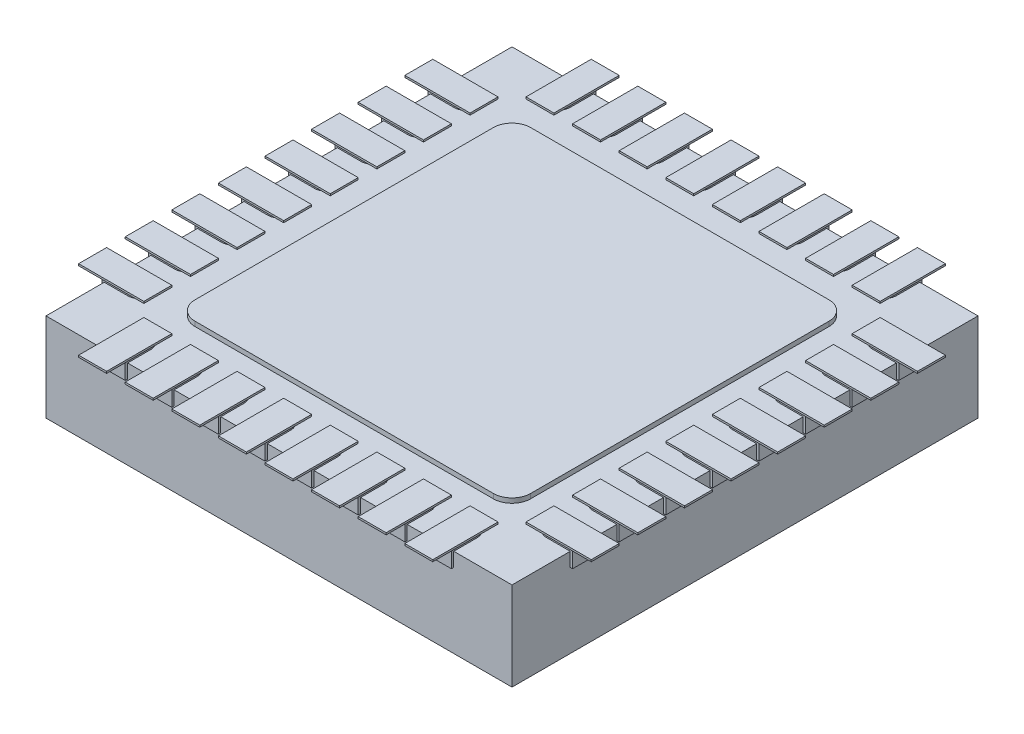
SolidWorks part; units mm, degrees
ref_plane "Front Plane" through (0, 0, 0) normal (0, 0, 1) x (1, 0, 0)
ref_plane "Top Plane" through (0, 0, 0) normal (0, 1, 0) x (1, 0, 0)
ref_plane "Right Plane" through (0, 0, 0) normal (1, 0, 0) x (0, 0, -1)
sketch "Sketch1" plane through (0, 0, 0) normal (0, 1, 0) x (1, 0, 0)
  line L0 (0, -2.75) -> (0, 2.75) construction
  line L1 (-2.525, 2.525) -> (2.525, 2.525)
  line L2 (-2.525, 2.525) -> (-2.525, -2.525)
  line L3 (-2.525, -2.525) -> (2.525, -2.525)
  line L4 (2.525, 2.525) -> (2.525, -2.525)
  line L5 (-2.75, 0) -> (2.75, 0) construction
sketch "Sketch2" plane through (0, 0, 0) normal (0, 1, 0) x (1, 0, 0)
  line L0 (0, -2.75) -> (0, 2.75) construction
  line L1 (-1.6, -1.8) -> (1.6, -1.8)
  line L2 (-1.8, -1.6) -> (-1.8, 1.6)
  line L3 (-1.6, 1.8) -> (1.6, 1.8)
  line L4 (1.8, -1.6) -> (1.8, 1.6)
  line L5 (-2.75, 0) -> (2.75, 0) construction
  line L6 (-1.875, -2.25) -> (-1.875, -2.525)
  line L8 (-1.875, -2.525) -> (-1.625, -2.525)
  line L9 (-1.625, -2.525) -> (-1.625, -2.25)
  line L10 (-1.875, 2.25) -> (-1.875, 2.525)
  line L12 (-1.875, 2.525) -> (-1.625, 2.525)
  line L13 (-1.625, 2.525) -> (-1.625, 2.25)
  line L14 (-1.375, -2.25) -> (-1.375, -2.525)
  line L15 (-1.125, -2.525) -> (-1.125, -2.25)
  line L16 (-1.375, -2.525) -> (-1.125, -2.525)
  line L17 (-1.125, 2.525) -> (-1.125, 2.25)
  line L18 (-1.375, 2.25) -> (-1.375, 2.525)
  line L19 (-1.375, 2.525) -> (-1.125, 2.525)
  line L20 (-0.875, -2.25) -> (-0.875, -2.525)
  line L21 (-0.625, -2.525) -> (-0.625, -2.25)
  line L22 (-0.875, -2.525) -> (-0.625, -2.525)
  line L23 (-0.625, 2.525) -> (-0.625, 2.25)
  line L24 (-0.875, 2.25) -> (-0.875, 2.525)
  line L25 (-0.875, 2.525) -> (-0.625, 2.525)
  line L26 (-0.375, -2.25) -> (-0.375, -2.525)
  line L27 (-0.125, -2.525) -> (-0.125, -2.25)
  line L28 (-0.375, -2.525) -> (-0.125, -2.525)
  line L29 (-0.125, 2.525) -> (-0.125, 2.25)
  line L30 (-0.375, 2.25) -> (-0.375, 2.525)
  line L31 (-0.375, 2.525) -> (-0.125, 2.525)
  line L32 (0.125, -2.25) -> (0.125, -2.525)
  line L33 (0.375, -2.525) -> (0.375, -2.25)
  line L34 (0.125, -2.525) -> (0.375, -2.525)
  line L35 (0.375, 2.525) -> (0.375, 2.25)
  line L36 (0.125, 2.25) -> (0.125, 2.525)
  line L37 (0.125, 2.525) -> (0.375, 2.525)
  line L38 (0.625, -2.25) -> (0.625, -2.525)
  line L39 (0.875, -2.525) -> (0.875, -2.25)
  line L40 (0.625, -2.525) -> (0.875, -2.525)
  line L41 (0.875, 2.525) -> (0.875, 2.25)
  line L42 (0.625, 2.25) -> (0.625, 2.525)
  line L43 (0.625, 2.525) -> (0.875, 2.525)
  line L44 (1.125, -2.25) -> (1.125, -2.525)
  line L45 (1.375, -2.525) -> (1.375, -2.25)
  line L46 (1.125, -2.525) -> (1.375, -2.525)
  line L47 (1.375, 2.525) -> (1.375, 2.25)
  line L48 (1.125, 2.25) -> (1.125, 2.525)
  line L49 (1.125, 2.525) -> (1.375, 2.525)
  line L50 (1.625, -2.25) -> (1.625, -2.525)
  line L51 (1.875, -2.525) -> (1.875, -2.25)
  line L52 (1.625, -2.525) -> (1.875, -2.525)
  line L53 (1.875, 2.525) -> (1.875, 2.25)
  line L54 (1.625, 2.25) -> (1.625, 2.525)
  line L55 (1.625, 2.525) -> (1.875, 2.525)
  line L56 (-2.525, -1.875) -> (-2.245, -1.875)
  line L59 (-2.245, -1.625) -> (-2.525, -1.625)
  line L60 (2.245, -1.875) -> (2.525, -1.875)
  line L62 (2.525, -1.875) -> (2.525, -1.625)
  line L63 (2.525, -1.625) -> (2.245, -1.625)
  line L64 (-2.525, -1.625) -> (-2.525, -1.875)
  line L65 (-2.245, -1.125) -> (-2.525, -1.125)
  line L66 (-2.525, -1.375) -> (-2.245, -1.375)
  line L67 (-2.525, -1.125) -> (-2.525, -1.375)
  line L68 (2.245, -1.375) -> (2.525, -1.375)
  line L69 (2.525, -1.375) -> (2.525, -1.125)
  line L70 (2.525, -1.125) -> (2.245, -1.125)
  line L71 (-2.245, -0.625) -> (-2.525, -0.625)
  line L72 (-2.525, -0.875) -> (-2.245, -0.875)
  line L73 (-2.525, -0.625) -> (-2.525, -0.875)
  line L74 (2.245, -0.875) -> (2.525, -0.875)
  line L75 (2.525, -0.875) -> (2.525, -0.625)
  line L76 (2.525, -0.625) -> (2.245, -0.625)
  line L77 (-2.245, -0.125) -> (-2.525, -0.125)
  line L78 (-2.525, -0.375) -> (-2.245, -0.375)
  line L79 (-2.525, -0.125) -> (-2.525, -0.375)
  line L80 (2.245, -0.375) -> (2.525, -0.375)
  line L81 (2.525, -0.375) -> (2.525, -0.125)
  line L82 (2.525, -0.125) -> (2.245, -0.125)
  line L83 (-2.245, 0.375) -> (-2.525, 0.375)
  line L84 (-2.525, 0.125) -> (-2.245, 0.125)
  line L85 (-2.525, 0.375) -> (-2.525, 0.125)
  line L86 (2.245, 0.125) -> (2.525, 0.125)
  line L87 (2.525, 0.125) -> (2.525, 0.375)
  line L88 (2.525, 0.375) -> (2.245, 0.375)
  line L89 (-2.245, 0.875) -> (-2.525, 0.875)
  line L90 (-2.525, 0.625) -> (-2.245, 0.625)
  line L91 (-2.525, 0.875) -> (-2.525, 0.625)
  line L92 (2.245, 0.625) -> (2.525, 0.625)
  line L93 (2.525, 0.625) -> (2.525, 0.875)
  line L94 (2.525, 0.875) -> (2.245, 0.875)
  line L95 (-2.245, 1.375) -> (-2.525, 1.375)
  line L96 (-2.525, 1.125) -> (-2.245, 1.125)
  line L97 (-2.525, 1.375) -> (-2.525, 1.125)
  line L98 (2.245, 1.125) -> (2.525, 1.125)
  line L99 (2.525, 1.125) -> (2.525, 1.375)
  line L100 (2.525, 1.375) -> (2.245, 1.375)
  line L101 (-2.245, 1.875) -> (-2.525, 1.875)
  line L102 (-2.525, 1.625) -> (-2.245, 1.625)
  line L103 (-2.525, 1.875) -> (-2.525, 1.625)
  line L104 (2.245, 1.625) -> (2.525, 1.625)
  line L105 (2.525, 1.625) -> (2.525, 1.875)
  line L106 (2.525, 1.875) -> (2.245, 1.875)
  line L107 (-2.245, -1.625) -> (-2.245, -1.125) construction
  line L108 (-2.525, 2.525) -> (-2.525, -2.525) construction
  line L109 (-2.525, 2.525) -> (2.525, 2.525) construction
  line L110 (-2.525, -2.525) -> (2.525, -2.525) construction
  line L111 (2.525, 2.525) -> (2.525, -2.525) construction
  arc A0 (1.6, 1.8) -> (1.8, 1.6) centre (1.6, 1.6) cw
  arc A1 (-1.8, 1.6) -> (-1.6, 1.8) centre (-1.6, 1.6) cw
  arc A2 (-1.6, -1.8) -> (-1.8, -1.6) centre (-1.6, -1.6) cw
  arc A3 (1.6, -1.8) -> (1.8, -1.6) centre (1.6, -1.6) ccw
  arc A4 (-1.625, -2.25) -> (-1.875, -2.25) centre (-1.75, -2.25) ccw
  arc A5 (-1.875, 2.25) -> (-1.625, 2.25) centre (-1.75, 2.25) ccw
  arc A6 (-1.125, -2.25) -> (-1.375, -2.25) centre (-1.25, -2.25) ccw
  arc A7 (-1.375, 2.25) -> (-1.125, 2.25) centre (-1.25, 2.25) ccw
  arc A8 (-0.625, -2.25) -> (-0.875, -2.25) centre (-0.75, -2.25) ccw
  arc A9 (-0.875, 2.25) -> (-0.625, 2.25) centre (-0.75, 2.25) ccw
  arc A10 (-0.125, -2.25) -> (-0.375, -2.25) centre (-0.25, -2.25) ccw
  arc A11 (-0.375, 2.25) -> (-0.125, 2.25) centre (-0.25, 2.25) ccw
  arc A12 (0.375, -2.25) -> (0.125, -2.25) centre (0.25, -2.25) ccw
  arc A13 (0.125, 2.25) -> (0.375, 2.25) centre (0.25, 2.25) ccw
  arc A14 (0.875, -2.25) -> (0.625, -2.25) centre (0.75, -2.25) ccw
  arc A15 (0.625, 2.25) -> (0.875, 2.25) centre (0.75, 2.25) ccw
  arc A16 (1.375, -2.25) -> (1.125, -2.25) centre (1.25, -2.25) ccw
  arc A17 (1.125, 2.25) -> (1.375, 2.25) centre (1.25, 2.25) ccw
  arc A18 (1.875, -2.25) -> (1.625, -2.25) centre (1.75, -2.25) ccw
  arc A19 (1.625, 2.25) -> (1.875, 2.25) centre (1.75, 2.25) ccw
  arc A20 (-2.245, -1.875) -> (-2.245, -1.625) centre (-2.245, -1.75) ccw
  arc A21 (2.245, -1.625) -> (2.245, -1.875) centre (2.245, -1.75) ccw
  arc A22 (-2.245, -1.375) -> (-2.245, -1.125) centre (-2.245, -1.25) ccw
  arc A23 (2.245, -1.125) -> (2.245, -1.375) centre (2.245, -1.25) ccw
  arc A24 (-2.245, -0.875) -> (-2.245, -0.625) centre (-2.245, -0.75) ccw
  arc A25 (2.245, -0.625) -> (2.245, -0.875) centre (2.245, -0.75) ccw
  arc A26 (-2.245, -0.375) -> (-2.245, -0.125) centre (-2.245, -0.25) ccw
  arc A27 (2.245, -0.125) -> (2.245, -0.375) centre (2.245, -0.25) ccw
  arc A28 (-2.245, 0.125) -> (-2.245, 0.375) centre (-2.245, 0.25) ccw
  arc A29 (2.245, 0.375) -> (2.245, 0.125) centre (2.245, 0.25) ccw
  arc A30 (-2.245, 0.625) -> (-2.245, 0.875) centre (-2.245, 0.75) ccw
  arc A31 (2.245, 0.875) -> (2.245, 0.625) centre (2.245, 0.75) ccw
  arc A32 (-2.245, 1.125) -> (-2.245, 1.375) centre (-2.245, 1.25) ccw
  arc A33 (2.245, 1.375) -> (2.245, 1.125) centre (2.245, 1.25) ccw
  arc A34 (-2.245, 1.625) -> (-2.245, 1.875) centre (-2.245, 1.75) ccw
  arc A35 (2.245, 1.875) -> (2.245, 1.625) centre (2.245, 1.75) ccw
  point P14 (-1.8, -1.8)
  point P17 (1.8, -1.8)
  dimension "D5" = 0.2
  dimension "D1" = 3.6
  dimension "D2" = 1.8
  dimension "D3" = 1.8
  dimension "D4" = 1.8
  dimension "D6" = 0.25
  dimension "D7" = 0.275
  dimension "D8" = 1.75
  dimension "D10" = 0.5
  dimension "D11" = 1.75
  dimension "D12" = 0.25
  dimension "D13" = 0.28
  dimension "D15" = 0.5
  dimension "D9" = 8
  dimension "D14" = 8
sketch "Sketch3" plane through (0, 0, 0) normal (0, 1, 0) x (1, 0, 0)
  line L0 (0, -2.7775) -> (0, 2.7775) construction
  line L1 (2.5, 2.5) -> (-2.5, 2.5)
  line L2 (2.5, 2.5) -> (2.5, -2.5)
  line L3 (2.5, -2.5) -> (-2.5, -2.5)
  line L4 (-2.5, 2.5) -> (-2.5, -2.5)
  line L5 (-2.7775, 0) -> (2.7775, 0) construction
  dimension "D1" = 5
  dimension "D2" = 2.5
  dimension "D3" = 2.5
  dimension "D4" = 2.5
extrude "Boss-Extrude2" add sketch "Sketch3" against normal blind 0.95
extrude "Boss-Extrude3" add sketch "Sketch2" along normal blind 0.05 and the other way blind 0.15
ref_plane "Plane1" through (0, 0.06, 0) normal (0, 1, 0) x (1, 0, 0)
sketch "Sketch4" plane through (0, 0.06, 0) normal (0, 1, 0) x (1, 0, 0)
  line L0 (-0.5555, 0) -> (0.5555, 0) construction
  line L1 (-1.9, 2.75) -> (-1.6, 2.75)
  line L2 (-1.9, 2.75) -> (-1.9, 2.05)
  line L3 (-1.9, 2.05) -> (-1.6, 2.05)
  line L4 (-1.6, 2.75) -> (-1.6, 2.05)
  line L5 (-1.9, -2.05) -> (-1.6, -2.05)
  line L6 (-1.9, -2.05) -> (-1.9, -2.75)
  line L7 (-1.9, -2.75) -> (-1.6, -2.75)
  line L8 (-1.6, -2.05) -> (-1.6, -2.75)
  line L9 (0, -0.5555) -> (0, 0.5555) construction
  line L10 (-1.4, -2.75) -> (-1.1, -2.75)
  line L11 (-1.1, -2.05) -> (-1.1, -2.75)
  line L12 (-1.4, -2.05) -> (-1.4, -2.75)
  line L13 (-1.4, -2.05) -> (-1.1, -2.05)
  line L14 (-1.4, 2.75) -> (-1.4, 2.05)
  line L15 (-1.4, 2.05) -> (-1.1, 2.05)
  line L16 (-1.1, 2.75) -> (-1.1, 2.05)
  line L17 (-1.4, 2.75) -> (-1.1, 2.75)
  line L18 (-0.9, -2.75) -> (-0.6, -2.75)
  line L19 (-0.6, -2.05) -> (-0.6, -2.75)
  line L20 (-0.9, -2.05) -> (-0.9, -2.75)
  line L21 (-0.9, -2.05) -> (-0.6, -2.05)
  line L22 (-0.9, 2.75) -> (-0.9, 2.05)
  line L23 (-0.9, 2.05) -> (-0.6, 2.05)
  line L24 (-0.6, 2.75) -> (-0.6, 2.05)
  line L25 (-0.9, 2.75) -> (-0.6, 2.75)
  line L26 (-0.4, -2.75) -> (-0.1, -2.75)
  line L27 (-0.1, -2.05) -> (-0.1, -2.75)
  line L28 (-0.4, -2.05) -> (-0.4, -2.75)
  line L29 (-0.4, -2.05) -> (-0.1, -2.05)
  line L30 (-0.4, 2.75) -> (-0.4, 2.05)
  line L31 (-0.4, 2.05) -> (-0.1, 2.05)
  line L32 (-0.1, 2.75) -> (-0.1, 2.05)
  line L33 (-0.4, 2.75) -> (-0.1, 2.75)
  line L34 (0.1, -2.75) -> (0.4, -2.75)
  line L35 (0.4, -2.05) -> (0.4, -2.75)
  line L36 (0.1, -2.05) -> (0.1, -2.75)
  line L37 (0.1, -2.05) -> (0.4, -2.05)
  line L38 (0.1, 2.75) -> (0.1, 2.05)
  line L39 (0.1, 2.05) -> (0.4, 2.05)
  line L40 (0.4, 2.75) -> (0.4, 2.05)
  line L41 (0.1, 2.75) -> (0.4, 2.75)
  line L42 (0.6, -2.75) -> (0.9, -2.75)
  line L43 (0.9, -2.05) -> (0.9, -2.75)
  line L44 (0.6, -2.05) -> (0.6, -2.75)
  line L45 (0.6, -2.05) -> (0.9, -2.05)
  line L46 (0.6, 2.75) -> (0.6, 2.05)
  line L47 (0.6, 2.05) -> (0.9, 2.05)
  line L48 (0.9, 2.75) -> (0.9, 2.05)
  line L49 (0.6, 2.75) -> (0.9, 2.75)
  line L50 (1.1, -2.75) -> (1.4, -2.75)
  line L51 (1.4, -2.05) -> (1.4, -2.75)
  line L52 (1.1, -2.05) -> (1.1, -2.75)
  line L53 (1.1, -2.05) -> (1.4, -2.05)
  line L54 (1.1, 2.75) -> (1.1, 2.05)
  line L55 (1.1, 2.05) -> (1.4, 2.05)
  line L56 (1.4, 2.75) -> (1.4, 2.05)
  line L57 (1.1, 2.75) -> (1.4, 2.75)
  line L58 (1.6, -2.75) -> (1.9, -2.75)
  line L59 (1.9, -2.05) -> (1.9, -2.75)
  line L60 (1.6, -2.05) -> (1.6, -2.75)
  line L61 (1.6, -2.05) -> (1.9, -2.05)
  line L62 (1.6, 2.75) -> (1.6, 2.05)
  line L63 (1.6, 2.05) -> (1.9, 2.05)
  line L64 (1.9, 2.75) -> (1.9, 2.05)
  line L65 (1.6, 2.75) -> (1.9, 2.75)
  line L66 (-1.9, -2.75) -> (-1.4, -2.75) construction
  line L67 (-2.75, 1.1) -> (-2.05, 1.1)
  line L68 (-2.75, 1.9) -> (-2.05, 1.9)
  line L69 (-2.75, 1.9) -> (-2.75, 1.6)
  line L70 (-2.75, 1.6) -> (-2.05, 1.6)
  line L71 (-2.05, 1.9) -> (-2.05, 1.6)
  line L72 (2.05, 1.9) -> (2.75, 1.9)
  line L73 (2.05, 1.9) -> (2.05, 1.6)
  line L74 (2.05, 1.6) -> (2.75, 1.6)
  line L75 (2.75, 1.9) -> (2.75, 1.6)
  line L76 (-2.05, 1.4) -> (-2.05, 1.1)
  line L77 (-2.75, 1.4) -> (-2.05, 1.4)
  line L78 (-2.75, 1.4) -> (-2.75, 1.1)
  line L79 (2.05, 1.4) -> (2.75, 1.4)
  line L80 (2.75, 1.4) -> (2.75, 1.1)
  line L81 (2.05, 1.1) -> (2.75, 1.1)
  line L82 (2.05, 1.4) -> (2.05, 1.1)
  line L83 (-2.75, 0.6) -> (-2.05, 0.6)
  line L84 (-2.05, 0.9) -> (-2.05, 0.6)
  line L85 (-2.75, 0.9) -> (-2.05, 0.9)
  line L86 (-2.75, 0.9) -> (-2.75, 0.6)
  line L87 (2.05, 0.9) -> (2.75, 0.9)
  line L88 (2.75, 0.9) -> (2.75, 0.6)
  line L89 (2.05, 0.6) -> (2.75, 0.6)
  line L90 (2.05, 0.9) -> (2.05, 0.6)
  line L91 (-2.75, 0.1) -> (-2.05, 0.1)
  line L92 (-2.05, 0.4) -> (-2.05, 0.1)
  line L93 (-2.75, 0.4) -> (-2.05, 0.4)
  line L94 (-2.75, 0.4) -> (-2.75, 0.1)
  line L95 (2.05, 0.4) -> (2.75, 0.4)
  line L96 (2.75, 0.4) -> (2.75, 0.1)
  line L97 (2.05, 0.1) -> (2.75, 0.1)
  line L98 (2.05, 0.4) -> (2.05, 0.1)
  line L99 (-2.75, -0.4) -> (-2.05, -0.4)
  line L100 (-2.05, -0.1) -> (-2.05, -0.4)
  line L101 (-2.75, -0.1) -> (-2.05, -0.1)
  line L102 (-2.75, -0.1) -> (-2.75, -0.4)
  line L103 (2.05, -0.1) -> (2.75, -0.1)
  line L104 (2.75, -0.1) -> (2.75, -0.4)
  line L105 (2.05, -0.4) -> (2.75, -0.4)
  line L106 (2.05, -0.1) -> (2.05, -0.4)
  line L107 (-2.75, -0.9) -> (-2.05, -0.9)
  line L108 (-2.05, -0.6) -> (-2.05, -0.9)
  line L109 (-2.75, -0.6) -> (-2.05, -0.6)
  line L110 (-2.75, -0.6) -> (-2.75, -0.9)
  line L111 (2.05, -0.6) -> (2.75, -0.6)
  line L112 (2.75, -0.6) -> (2.75, -0.9)
  line L113 (2.05, -0.9) -> (2.75, -0.9)
  line L114 (2.05, -0.6) -> (2.05, -0.9)
  line L115 (-2.75, -1.4) -> (-2.05, -1.4)
  line L116 (-2.05, -1.1) -> (-2.05, -1.4)
  line L117 (-2.75, -1.1) -> (-2.05, -1.1)
  line L118 (-2.75, -1.1) -> (-2.75, -1.4)
  line L119 (2.05, -1.1) -> (2.75, -1.1)
  line L120 (2.75, -1.1) -> (2.75, -1.4)
  line L121 (2.05, -1.4) -> (2.75, -1.4)
  line L122 (2.05, -1.1) -> (2.05, -1.4)
  line L123 (-2.75, -1.9) -> (-2.05, -1.9)
  line L124 (-2.05, -1.6) -> (-2.05, -1.9)
  line L125 (-2.75, -1.6) -> (-2.05, -1.6)
  line L126 (-2.75, -1.6) -> (-2.75, -1.9)
  line L127 (2.05, -1.6) -> (2.75, -1.6)
  line L128 (2.75, -1.6) -> (2.75, -1.9)
  line L129 (2.05, -1.9) -> (2.75, -1.9)
  line L130 (2.05, -1.6) -> (2.05, -1.9)
  line L131 (-2.75, 1.6) -> (-2.75, 1.1) construction
  dimension "D1" = 0.3
  dimension "D2" = 0.7
  dimension "D3" = 5.5
  dimension "D4" = 2.75
  dimension "D5" = 1.9
  dimension "D7" = 0.5
  dimension "D8" = 2.75
  dimension "D9" = 5.5
  dimension "D10" = 1.9
  dimension "D11" = 0.3
  dimension "D12" = 0.7
  dimension "D14" = 0.5
  dimension "D6" = 8
  dimension "D13" = 8
extrude "Boss-Extrude4" add sketch "Sketch4" against normal blind 0.02
sketch "Sketch5" plane through (0, -0.95, 0) normal (0, -1, 0) x (1, 0, 0)
  line L0 (-1.0975, -0.97) -> (-0.81, -0.97)
  line L1 (1.2, -0.925) -> (-1.0725, -0.925)
  line L2 (-0.9755, -0.75) -> (-1.0725, -0.925)
  line L3 (-0.76, -1.155) -> (-0.495, -1.155)
  line L4 (-1.2, -1.155) -> (-1, -1.155)
  line L5 (-0.76, -1.2) -> (-0.495, -1.2)
  line L6 (-0.76, -1.385) -> (-0.495, -1.385)
  line L7 (-0.76, -1.43) -> (-0.495, -1.43)
  line L8 (-1.2, -1.67) -> (0.42, -1.67)
  line L9 (-1.2, -1.88) -> (0.6956, -1.88)
  line L10 (1.2, -0.97) -> (0.8425, -1.615)
  line L11 (-0.2, -1.615) -> (0.37, -1.615)
  line L12 (0.91, -0.97) -> (0.91, -1.045)
  line L13 (-0.9755, -0.75) -> (1.2, -0.75)
  line L14 (1.2, -0.75) -> (1.2, -0.925)
  line L15 (0.91, -1.045) -> (0.965, -1.045)
  line L16 (0.965, -1.045) -> (0.86, -1.2344)
  line L17 (0.86, -1.2344) -> (0.86, -0.97)
  line L18 (-0.81, -0.97) -> (-0.81, -1.615)
  line L19 (-0.76, -0.97) -> (-0.76, -1.615)
  line L20 (-0.35, -0.97) -> (-0.35, -1.615)
  line L21 (-0.3, -0.97) -> (-0.3, -1.515)
  line L22 (-0.11, -0.97) -> (-0.11, -1.515)
  line L23 (-0.06, -0.97) -> (-0.06, -1.545)
  line L24 (0.13, -0.97) -> (0.13, -1.535)
  line L25 (0.18, -0.97) -> (0.18, -1.535)
  line L26 (0.37, -0.97) -> (0.37, -1.615)
  line L27 (0.42, -0.97) -> (0.42, -1.67)
  line L28 (0.62, -0.97) -> (0.62, -1.67)
  line L29 (0.67, -0.97) -> (0.67, -1.615)
  line L30 (0.17, -1.545) -> (0.14, -1.545)
  line L31 (-0.06, -1.545) -> (-0.08, -1.545)
  line L32 (-0.35, -1.615) -> (-0.76, -1.615)
  line L33 (-1, -1.155) -> (-1, -1.615)
  line L34 (-1.0975, -0.97) -> (-1.2, -1.155)
  line L35 (-0.48, -1.17) -> (-0.48, -1.185)
  line L36 (0.67, -1.615) -> (0.8425, -1.615)
  line L37 (0.62, -1.67) -> (0.812, -1.67)
  line L38 (-0.76, -0.97) -> (-0.35, -0.97)
  line L39 (-0.3, -0.97) -> (-0.11, -0.97)
  line L40 (-0.48, -1.4) -> (-0.48, -1.415)
  line L41 (-0.81, -1.615) -> (-1, -1.615)
  line L42 (-1.2, -1.67) -> (-1.2, -1.88)
  line L43 (0.812, -1.67) -> (0.6956, -1.88)
  line L44 (-0.06, -0.97) -> (0.13, -0.97)
  line L45 (0.18, -0.97) -> (0.37, -0.97)
  line L46 (0.42, -0.97) -> (0.62, -0.97)
  line L47 (0.67, -0.97) -> (0.86, -0.97)
  line L48 (0.91, -0.97) -> (1.2, -0.97)
  line L49 (0.5555, 0) -> (-0.5555, 0) construction
  line L50 (0, -0.5555) -> (0, 0.5555) construction
  line L51 (2.5, 2.5) -> (2.5, -2.5) construction
  line L52 (-2.5, -2.5) -> (-2.5, 2.5) construction
  arc A0 (-0.2, -1.615) -> (-0.3, -1.515) centre (-0.2, -1.515) cw
  arc A1 (-0.08, -1.545) -> (-0.11, -1.515) centre (-0.08, -1.515) cw
  arc A2 (0.17, -1.545) -> (0.18, -1.535) centre (0.17, -1.535) ccw
  arc A3 (0.13, -1.535) -> (0.14, -1.545) centre (0.14, -1.535) ccw
  arc A4 (-0.495, -1.43) -> (-0.48, -1.415) centre (-0.495, -1.415) ccw
  arc A5 (-0.48, -1.4) -> (-0.495, -1.385) centre (-0.495, -1.4) ccw
  arc A6 (-0.495, -1.2) -> (-0.48, -1.185) centre (-0.495, -1.185) ccw
  arc A7 (-0.48, -1.17) -> (-0.495, -1.155) centre (-0.495, -1.17) ccw
  dimension "D25" = 0.1
  dimension "D26" = 0.03
  dimension "D28" = 0.01
  dimension "D33" = 0.015
  dimension "D1" = 0.045
  dimension "D2" = 0.045
  dimension "D3" = 0.045
  dimension "D4" = 0.055
  dimension "D5" = 61
  dimension "D6" = 0.075
  dimension "D7" = 0.055
  dimension "D8" = 0.185
  dimension "D9" = 0.185
  dimension "D10" = 0.185
  dimension "D11" = 0.21
  dimension "D12" = 0.05
  dimension "D13" = 0.05
  dimension "D14" = 0.05
  dimension "D15" = 0.05
  dimension "D16" = 0.05
  dimension "D17" = 0.05
  dimension "D18" = 0.53
  dimension "D19" = 0.2
  dimension "D20" = 0.19
  dimension "D21" = 0.19
  dimension "D22" = 0.19
  dimension "D23" = 0.41
  dimension "D24" = 2.4
  dimension "D27" = 0.07
  dimension "D29" = 0.19
  dimension "D30" = 0.19
  dimension "D31" = 0.05
  dimension "D32" = 0.28
  dimension "D34" = 0.75
  dimension "D35" = 1.2
  dimension "D36" = 0.175
  dimension "D37" = 1.3
  dimension "D38" = 1.3
sketch "Sketch6" plane through (0, -0.95, 0) normal (0, -1, 0) x (1, 0, 0)
  line L0 (1.3, 0.1) -> (-2.5795, 0.1) construction
  line L1 (1.3, 1.9) -> (-2.5795, 1.9) construction
  line L2 (1.3, 1) -> (-2.5795, 1) construction
  line L3 (0, -0.5555) -> (0, 0.5555) construction
  line L4 (0.5555, 0) -> (-0.5555, 0) construction
  text T0 "MEGA16U2" font "SWRomnd" height 0.55
  text T1 "0928 PH" font "SWRomnd" height 0.55
  text T2 "9F3451" font "SWRomnd" height 0.55
  dimension "D1" = 1.3
  dimension "D2" = 0.1
  dimension "D3" = 0.9
  dimension "D4" = 0.9
extrude "Cut-Extrude1" cut sketch "Sketch6" against normal blind 0.05
extrude "Cut-Extrude2" cut sketch "Sketch5" against normal blind 0.05 contours L41 L18 L0 L34 L4 L33 | A7 L35 A6 L5 L19 L6 A5 L40 A4 L7 L32 L20 L38 L3 | A3 L24 L44 L23 L31 A1 L22 L39 L21 A0 L11 L26 L45 L25 A2 L30 | L14 L13 L2 L1 | L46 L27 L8 L42 L9 L43 L37 L28 | L48 L12 L15 L16 L17 L47 L29 L36 L10
sketch "Sketch7" plane through (0, -0.95, 0) normal (0, -1, 0) x (1, 0, 0)
  line L0 (0, -0.5555) -> (0, 0.5555) construction
  line L1 (0.5555, 0) -> (-0.5555, 0) construction
  circle A0 centre (1.75, -1.75) radius 0.3
  dimension "D1" = 0.6
  dimension "D2" = 1.75
  dimension "D3" = 1.75
extrude "Cut-Extrude3" cut sketch "Sketch7" against normal blind 0.1
equation "\"D2@Sketch1\"=\"D1@Sketch1\"/2"
equation "\"D3@Sketch1\"=\"D1@Sketch1\"/2"
